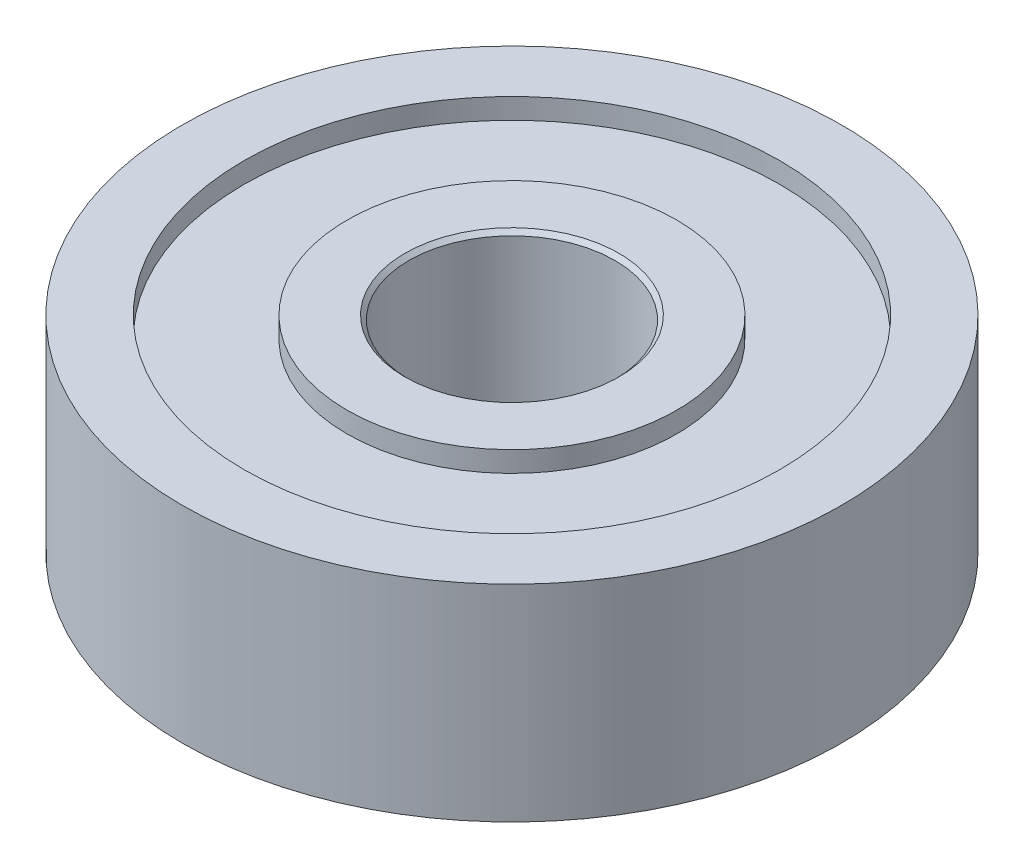
SolidWorks part; units mm, degrees
ref_plane "Front Plane" through (0, 0, 0) normal (0, 0, 1) x (1, 0, 0)
ref_plane "Top Plane" through (0, 0, 0) normal (0, 1, 0) x (1, 0, 0)
ref_plane "Right Plane" through (0, 0, 0) normal (1, 0, 0) x (0, 0, -1)
sketch "Sketch1" plane through (0, 0, 0) normal (0, 1, 0) x (1, 0, 0)
  circle A0 centre (0, 0) radius 8
  circle A1 centre (0, 0) radius 2.5
  dimension "D1" = 16
  dimension "D2" = 5
extrude "Boss-Extrude1" add sketch "Sketch1" along normal mid plane 5
sketch "Sketch2" plane through (0, 2.5, 0) normal (0, 1, 0) x (1, 0, 0)
  circle A0 centre (0, 0) radius 4
  circle A1 centre (0, 0) radius 6.5
  circle A2 centre (0, 0) radius 8 construction
  circle A3 centre (0, 0) radius 2.5 construction
  dimension "D1" = 1.5
  dimension "D2" = 1.5
extrude "Cut-Extrude1" cut sketch "Sketch2" against normal blind 0.5
mirror "Mirror1" about plane through (0, 0, 0) normal (0, 1, 0) of "Cut-Extrude1"
chamfer "Chamfer1" distance 0.1 angle 45 2 edges at (0, 2.5, 2.5) (0, -2.5, 2.5)
